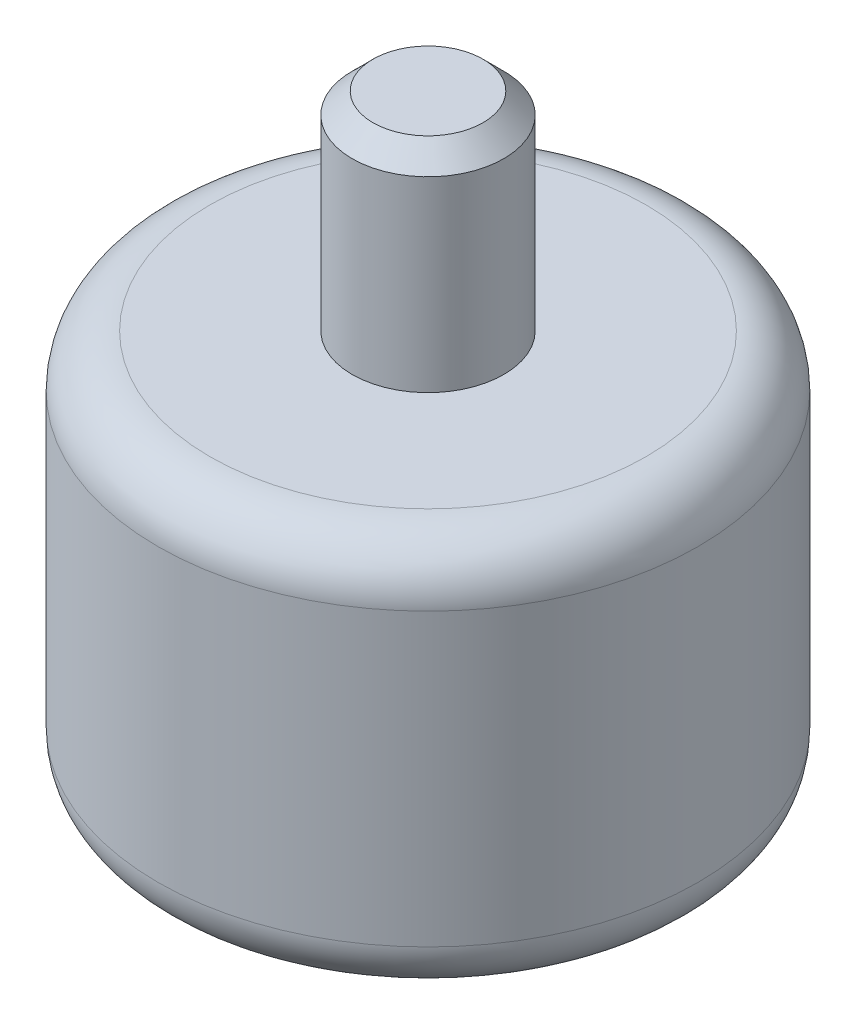
SolidWorks part; units mm, degrees
material "6061 Alloy"
ref_plane "Front Plane" through (0, 0, 0) normal (0, 0, 1) x (1, 0, 0)
ref_plane "Top Plane" through (0, 0, 0) normal (0, 1, 0) x (1, 0, 0)
ref_plane "Right Plane" through (0, 0, 0) normal (1, 0, 0) x (0, 0, -1)
sketch "Sketch1" plane through (0, 0, 0) normal (0, 1, 0) x (1, 0, 0)
  circle A0 centre (0, 0) radius 130
  dimension "D1" = 260
extrude "Boss-Extrude1" add sketch "Sketch1" along normal blind 190
fillet "Fillet1" radius 25 2 edges at (0, 190, 130) (0, 0, 130)
sketch "Sketch2" plane through (0, 0, 0) normal (0, -1, 0) x (1, 0, 0)
  circle A0 centre (0, 0) radius 36.5
  dimension "D1" = 73
extrude "Boss-Extrude2" add sketch "Sketch2" along normal blind 20
sketch "Sketch3" plane through (0, 0, 0) normal (0, -1, 0) x (1, 0, 0)
  circle A0 centre (95, 0) radius 4
  circle A1 centre (0, -95) radius 4
  circle A2 centre (-95, 0) radius 4
  circle A3 centre (0, 95) radius 4
  point P12 (0, 0)
  dimension "D2" = 8
  dimension "D1" = 95
  dimension "D3" = 4
hole_wizard "M8 Tapped Hole2" positions "Sketch6" profile "Sketch7" tap size "M8" standard "ISO"
sketch "Sketch6" plane through (0, 0, 0) normal (0, -1, 0) x (-1, 0, 0)
  point P0 (0, -95)
  point P3 (-95, 0)
  point P6 (0, 95)
  point P9 (95, 0)
sketch "Sketch7" plane through (0, 0, 95) normal (1, 0, 0) x (0, 0, -1)
  line L0 (0, 0) -> (0, 19.75)
  line L1 (0, 19.75) -> (3.4, 17.7071)
  line L2 (3.4, 17.7071) -> (3.4, 0)
  line L5 (3.4, 0) -> (0, 0)
  line L10 (0, 19.75) -> (-3.4, 17.7071) construction
  line L11 (0, -6.35) -> (0, 107.95) construction
  dimension "Tap Drill Dia." = 6.8
  dimension "Tap Drill Depth" = 19.75
  dimension "Drill Angle" = 118
cosmetic thread "Hole Thread1" parameters "D1"=16, "D2"=8
cosmetic thread "Hole Thread2" parameters "D1"=16, "D2"=8
cosmetic thread "Hole Thread3" parameters "D1"=16, "D2"=8
cosmetic thread "Hole Thread4" parameters "D1"=16, "D2"=8
sketch "Sketch8" plane through (0, 190, 0) normal (0, 1, 0) x (1, 0, 0)
  circle A0 centre (0, 0) radius 36.5
  dimension "D1" = 73
extrude "Boss-Extrude3" add sketch "Sketch8" along normal blind 100
chamfer "Chamfer1" distance 10 angle 45 1 edges at (0, 290, 36.5)
